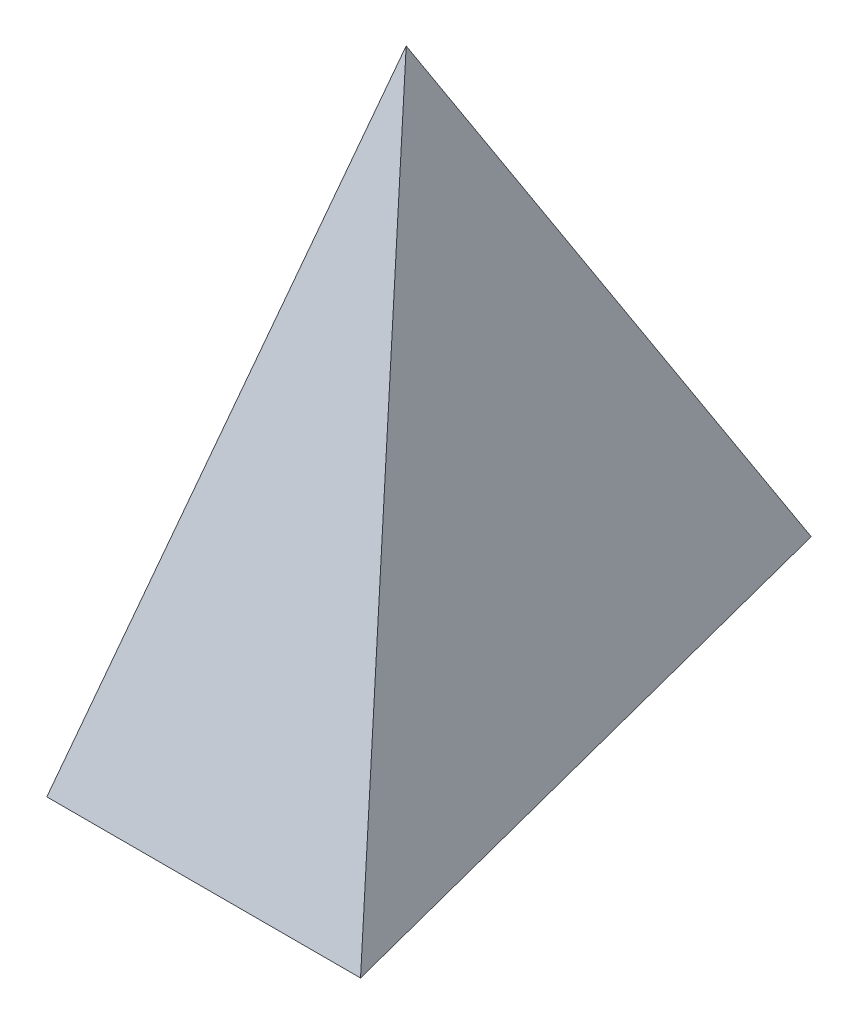
SolidWorks part; units mm, degrees
ref_plane "Front" through (0, 0, 0) normal (0, 0, 1) x (1, 0, 0)
ref_plane "Top" through (0, 0, 0) normal (0, 1, 0) x (1, 0, 0)
ref_plane "Right" through (0, 0, 0) normal (1, 0, 0) x (0, 0, -1)
sketch "Sketch1" plane through (0, 0, 0) normal (0, 1, 0) x (1, 0, 0)
  line L0 (0, 0) -> (10, 0)
  line L1 (10, 0) -> (5, 19.3649)
  line L2 (5, 19.3649) -> (0, 0)
  line L3 (5, 19.3649) -> (5, 0) construction
  line L4 (10, 0) -> (2.5, 9.6825) construction
  point P6 (5, 6.455)
  dimension "D1" = 10
  dimension "D2" = 20
ref_plane "Plane1" through (0, 0, -6.455) normal (0, 0, 1) x (1, 0, 0)
sketch "Sketch2" plane through (0, 0, -6.455) normal (0, 0, 1) x (1, 0, 0)
  point P0 (5, 20)
  dimension "D1" = 20
loft "Loft1" add profiles "Sketch2", "Sketch1"
